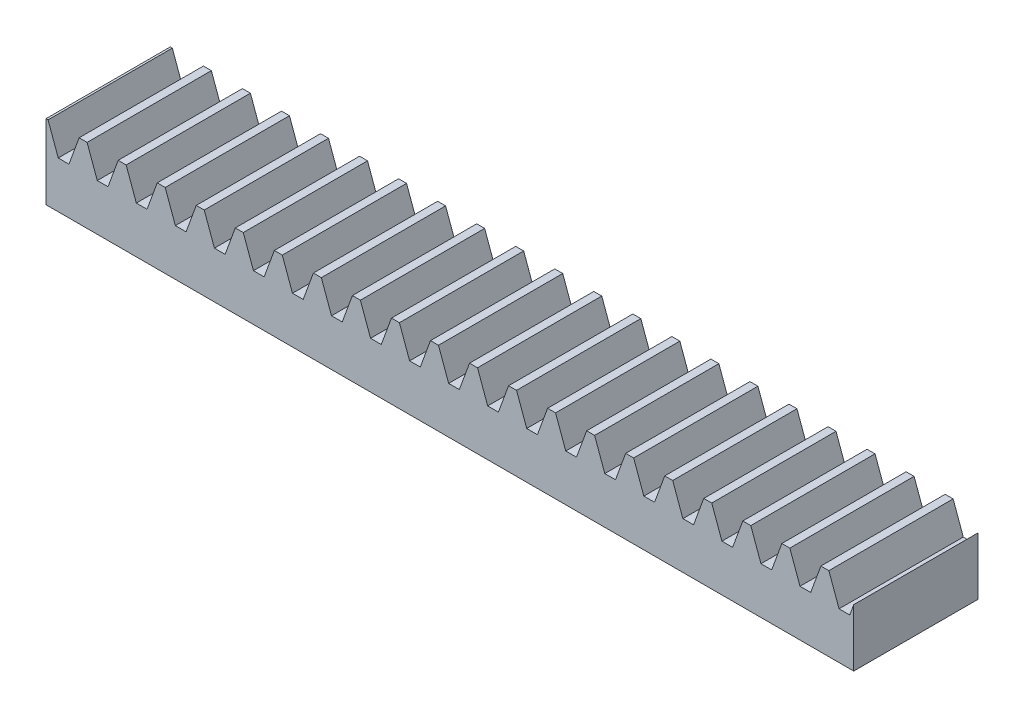
SolidWorks part; units mm, degrees
extrude "Blank" add sketch "BlankSke" against normal blind 20
sketch "BlankSke" plane through (0, 0, 0) normal (0, 0, 1) x (1, 0, 0)
  line L1 (0, 0) -> (250, 0)
  line L2 (0, 0) -> (0, 12)
  line L3 (0, 12) -> (250, 12)
  line L4 (250, 0) -> (250, 12)
  dimension "Length" = 250
  dimension "Blank_height" = 12
ref_plane "Plane1" through (0, 0, 0) normal (0, 0, 1) x (1, 0, 0)
ref_plane "Plane2" through (0, 0, 0) normal (0, 1, 0) x (1, 0, 0)
ref_plane "Plane3" through (0, 0, 0) normal (1, 0, 0) x (0, 0, -1)
sketch "HoldingSke" plane through (0, 0, 0) normal (0, 1, 0) x (1, 0, 0)
  line L0 (0, 0) -> (0.0696, 0.4951)
  line L1 (-15, 0) -> (100, 0) construction
  line L2 (0, 0) -> (-2.1039, 2.3779)
  line L3 (0, 0) -> (-11.863, 4.5341)
  line L4 (0, 0) -> (6.5177, 5.6657)
  line L5 (0, 0) -> (-23.7986, -8.8762)
  line L6 (0, 0) -> (-10.5278, -7.1032)
  line L9 (-71.009, 38.7566) -> (163.9142, 124.2616)
  line L10 (-76.2, 4.3779) -> (-66.2, 4.3779)
  line L11 (0, 0) -> (-20, 0)
  line L12 (-76.2, 101.6) -> (-76.133, 101.6)
  line L13 (24.9733, 27.94) -> (52.9518, 28.4284)
  line L14 (24.9733, 27.94) -> (24.9743, 27.94)
  line L15 (24.9733, 27.94) -> (100.4006, 29.5858)
  circle A0 centre (0, 0) radius 19.05
  circle A1 centre (0, 0) radius 5
  circle A2 centre (0, 0) radius 12.7
  dimension "MPH" = 10
  dimension "Diameter" = 38.1
  dimension "Num_teeth" = 41
  dimension "Pitch" = 0.5
  dimension "Show_teeth" = 998
  dimension "Thickness" = 12.7
  dimension "Ap" = 20
  dimension "Pitch_height" = 10
  dimension "Width" = 20
  dimension "Backlash" = 0.067
  dimension "Addendum_fac" = 1
  dimension "Dedendum_fac" = 1.25
  dimension "Clearance_fac" = 0.25
  dimension "Dedendum_add" = 0.001
  dimension "Length" = 250
  dimension "Module" = 2
sketch "TooCutSkeIll" plane through (0, 0, 0) normal (0, 0, 1) x (1, 0, 0)
  line L0 (-2.4806, 11.9474) -> (-0.9819, 7.8296)
  line L1 (-0.5111, 7.5) -> (0.5111, 7.5)
  line L2 (0.9819, 7.8296) -> (2.4806, 11.9474)
  line L3 (250, 12) -> (0, 12) construction
  line L4 (0, 0) -> (0, 64.897) construction
  line L5 (-13.208, 10) -> (12.954, 10) construction
  line L6 (0, 0) -> (250, 0) construction
  line L7 (1.7718, 10) -> (1.7718, 48.7463) construction
  line L8 (-1.7718, 10) -> (-1.7718, 48.7463) construction
  line L9 (2.5558, 12) -> (2.5558, 12.0254)
  line L10 (-2.5558, 12) -> (-2.5558, 12.0254)
  line L11 (-2.5558, 12.0254) -> (2.5558, 12.0254)
  arc A0 (0.5111, 7.5) -> (0.9819, 7.8296) centre (0.5111, 8.001) ccw
  arc A1 (-0.9819, 7.8296) -> (-0.5111, 7.5) centre (-0.5111, 8.001) ccw
  arc A2 (2.5558, 12) -> (2.4806, 11.9474) centre (2.5558, 11.92) ccw
  arc A3 (-2.4806, 11.9474) -> (-2.5558, 12) centre (-2.5558, 11.92) ccw
  dimension "Pitch_height" = 10
  dimension "Addendum_plus" = 2.0254
  dimension "Pressure_angle" = 20
  dimension "Gap_width" = 3.5436
  dimension "Dedendum" = 2.5
extrude "ToothCutIll" [suppressed] cut sketch "TooCutSkeIll" against normal through all
sketch "TooCutSkeSim" plane through (0, 0, 0) normal (0, 0, 1) x (1, 0, 0)
  line L0 (0.8619, 7.5) -> (-0.8619, 7.5)
  line L1 (2.509, 12.0254) -> (0.8619, 7.5)
  line L2 (0, 17.4625) -> (0, 53.467) construction
  line L3 (2.509, 12.0254) -> (-2.509, 12.0254)
  line L6 (-2.509, 12.0254) -> (-0.8619, 7.5)
  line L9 (-1.7718, 10) -> (1.7718, 10) construction
  line L10 (0, 0) -> (250, 0) construction
  line L11 (1.7718, 10) -> (1.7718, 53.467) construction
  line L12 (-1.7718, 10) -> (-1.7718, 53.467) construction
  dimension "Pitch_height" = 10
  dimension "Addendum_plus" = 2.0254
  dimension "Pressure_angle" = 20
  dimension "Gap_width" = 3.5436
  dimension "Dedendum" = 2.5
extrude "ToothCutSim" cut sketch "TooCutSkeSim" against normal through all
pattern_linear "TeethCuts" count 40 spacing 6.2832 along (1, 0, 0) of "ToothCutIll", "ToothCutSim"
sketch "Sketch1" plane through (0, 0, 0) normal (-1, 0, 0) x (0, 0, 1)
  line L1 (-21.191, -4.8116) -> (3.9767, -4.8116)
  line L2 (-21.191, -4.8116) -> (-21.191, 18.5037)
  line L3 (-21.191, 18.5037) -> (3.9767, 18.5037)
  line L4 (3.9767, -4.8116) -> (3.9767, 18.5037)
extrude "Cut-Extrude1" cut sketch "Sketch1" against normal blind 60
sketch "Sketch2" plane through (250, 0, 0) normal (1, 0, 0) x (0, 0, -1)
  line L1 (-11.5827, 24.579) -> (33.606, 24.579)
  line L2 (-11.5827, 24.579) -> (-11.5827, -14.1575)
  line L3 (-11.5827, -14.1575) -> (33.606, -14.1575)
  line L4 (33.606, 24.579) -> (33.606, -14.1575)
extrude "Cut-Extrude2" cut sketch "Sketch2" against normal blind 60
equation "' \"Module@HoldingSke\" = 6.35"
equation "' \"Num_teeth@HoldingSke\" = 12"
equation "' \"Ap@HoldingSke\" =  20"
equation "' \"Ap@HoldingSke\" = 20"
equation "' \"Width@HoldingSke\" = 0.25 * 25.4"
equation "' \"Show_teeth@HoldingSke\" = 500"
equation "' \"Backlash@HoldingSke\" = 0.009 * 25.4"
equation "' \"Addendum_fac@HoldingSke\" = 1.0"
equation "' \"Dedendum_fac@HoldingSke\" = 1.25"
equation "' \"Dedendum_add@HoldingSke\" = 0.00005 * 25.4"
equation "' \"Clearance_fac@HoldingSke\" = 0.25"
equation "' \"Pitch_height@HoldingSke\" = 1 * 25.4"
equation "' \"Length@HoldingSke\" = 4.71 * 25.4"
equation "\"Pitch@HoldingSke\" = 1 / \"Module@HoldingSke\""
equation "\"MPH@HoldingSke\" = \"Dedendum_fac@HoldingSke\" / \"Pitch@HoldingSke\" + 2 * \"Dedendum_add@HoldingSke\" + 0.002 * 25.4"
equation "\"MPH@HoldingSke\" = ((sgn( \"MPH@HoldingSke\" - \"Pitch_height@HoldingSke\")+1)*( \"MPH@HoldingSke\" - \"Pitch_height@HoldingSke\"))/2 + \"Pitch_height@HoldingSke\""
equation "\"Blank_height@BlankSke\" = \"Pitch_height@HoldingSke\" + \"Addendum_fac@HoldingSke\"  / \"Pitch@HoldingSke\" "
equation "\"Length@BlankSke\" =  \"Length@HoldingSke\""
equation "\"Face_width@Blank\" = \"Width@HoldingSke\""
equation "\"Pressure_angle@TooCutSkeIll\" = \"Ap@HoldingSke\""
equation "\"Addendum_plus@TooCutSkeIll\" =  \"Addendum_fac@HoldingSke\"  / \"Pitch@HoldingSke\" + 0.001 *25.4"
equation "\"Dedendum@TooCutSkeIll\" = \"Dedendum_fac@HoldingSke\"  / \"Pitch@HoldingSke\""
equation "\"Pitch_height@TooCutSkeIll\" =  \"MPH@HoldingSke\""
equation "\"Gap_width@TooCutSkeIll\" = 3.14159265 / 2 / \"Pitch@HoldingSke\" + 6 * \"Backlash@HoldingSke\""
equation "\"Pressure_angle@TooCutSkeSim\" = \"Ap@HoldingSke\""
equation "\"Addendum_plus@TooCutSkeSim\" =  \"Addendum_fac@HoldingSke\"  / \"Pitch@HoldingSke\" + 0.001 * 25.4"
equation "\"Dedendum@TooCutSkeSim\" = \"Dedendum_fac@HoldingSke\"  / \"Pitch@HoldingSke\""
equation "\"Pitch_height@TooCutSkeSim\" =  \"MPH@HoldingSke\""
equation "\"Gap_width@TooCutSkeSim\" = 3.14159265 / 2 / \"Pitch@HoldingSke\" + 6 * \"Backlash@HoldingSke\""
equation "\"Root_fillet@TooCutSkeIll\" = \"Clearance_fac@HoldingSke\" / \"Pitch@HoldingSke\" + \"Dedendum_add@HoldingSke\""
equation "\"Break_rad@TooCutSkeIll\" = 0.02 / \"Pitch@HoldingSke\" * 2"
equation "\"Linear_pitch@TeethCuts\" = 3.14159265 / \"Pitch@HoldingSke\""
equation "\"Num_teeth@HoldingSke\" = int( ( \"Length@HoldingSke\" + 0 ) / (3.14159265 / \"Pitch@HoldingSke\")) + 0.9999  + 1"
equation " \"Num_teeth@TeethCuts\" = int( \"Show_teeth@HoldingSke\" ) + 1"
equation " \"Num_teeth@TeethCuts\" = ((sgn( \"Num_teeth@TeethCuts\" - \"Num_teeth@HoldingSke\" )-1)*( \"Num_teeth@TeethCuts\" - \"Num_teeth@HoldingSke\" ))/-2+ \"Num_teeth@HoldingSke\""
equation " \"Num_teeth@TeethCuts\" = ((sgn( \"Num_teeth@TeethCuts\" - 2.0)+1)*( \"Num_teeth@TeethCuts\" - 2.0))/2 +2.0"
